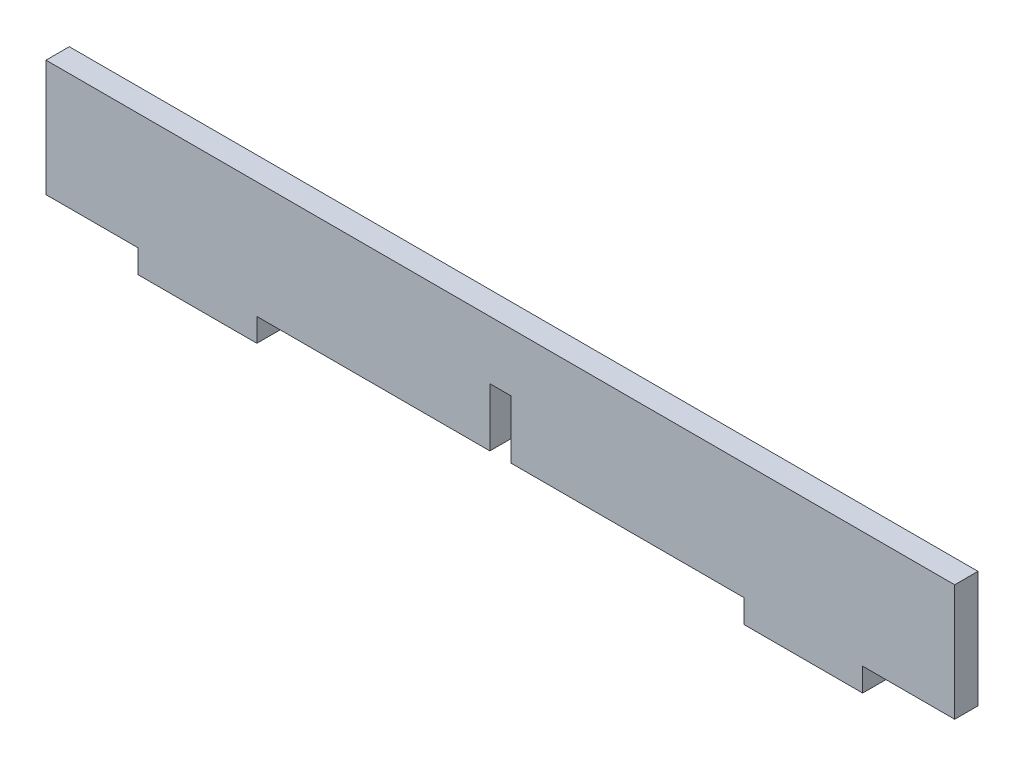
SolidWorks part; units mm, degrees
ref_plane "前基準面" through (0, 0, 0) normal (0, 0, 1) x (1, 0, 0)
ref_plane "上基準面" through (0, 0, 0) normal (0, 1, 0) x (1, 0, 0)
ref_plane "右基準面" through (0, 0, 0) normal (1, 0, 0) x (0, 0, -1)
sketch "草圖1" plane through (0, 0, 0) normal (0, 0, 1) x (1, 0, 0)
  line L0 (0, 0) -> (0, 24.9222) construction
  line L1 (-39, 2) -> (-31.1, 2)
  line L2 (-39, 2) -> (-39, 12)
  line L3 (-39, 12) -> (39, 12)
  line L4 (39, 2) -> (39, 12)
  line L5 (0.9, 2) -> (20.9, 2)
  line L6 (31.1, 2) -> (31.1, 0)
  line L7 (31.1, 0) -> (20.9, 0)
  line L8 (20.9, 2) -> (20.9, 0)
  line L9 (31.1, 2) -> (39, 2)
  line L10 (-20.9, 2) -> (-20.9, 0)
  line L11 (-20.9, 0) -> (-31.1, 0)
  line L12 (-31.1, 2) -> (-31.1, 0)
  line L13 (-11.3843, 0) -> (12.3473, 0) construction
  line L14 (-20.9, 2) -> (-0.9, 2)
  line L16 (-0.9, 2) -> (-0.9, 7)
  line L17 (-0.9, 7) -> (0.9, 7)
  line L18 (0.9, 2) -> (0.9, 7)
  dimension "D1" = 10
  dimension "D2" = 41.8
  dimension "D3" = 62.2
  dimension "D4" = 2
  dimension "D5" = 78
  dimension "D6" = 1.8
  dimension "D7" = 5
extrude "填料-伸長1" add sketch "草圖1" along normal blind 2
